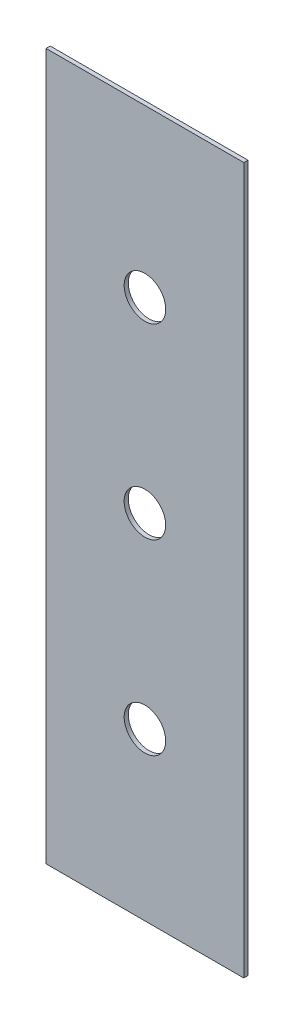
SolidWorks part; units mm, degrees
ref_plane "Plano frontal" through (0, 0, 0) normal (0, 0, 1) x (1, 0, 0)
ref_plane "Plano superior" through (0, 0, 0) normal (0, 1, 0) x (1, 0, 0)
ref_plane "Plano direito" through (0, 0, 0) normal (1, 0, 0) x (0, 0, -1)
sketch "Esboço1" plane through (0, 0, 0) normal (0, 0, 1) x (-1, 0, 0)
  line L0 (-299.6374, -35) -> (-252.0468, -35)
  line L1 (-252.0468, -35) -> (-252.0468, -205)
  line L2 (-252.0468, -205) -> (-299.6374, -205)
  line L3 (-299.6374, -205) -> (-299.6374, -35)
  circle A0 centre (-275.8421, -165) radius 5
  circle A1 centre (-275.8421, -120) radius 5
  circle A2 centre (-275.8421, -75) radius 5
extrude "Ressalto-extrusão1" add sketch "Esboço1" along normal blind 1
